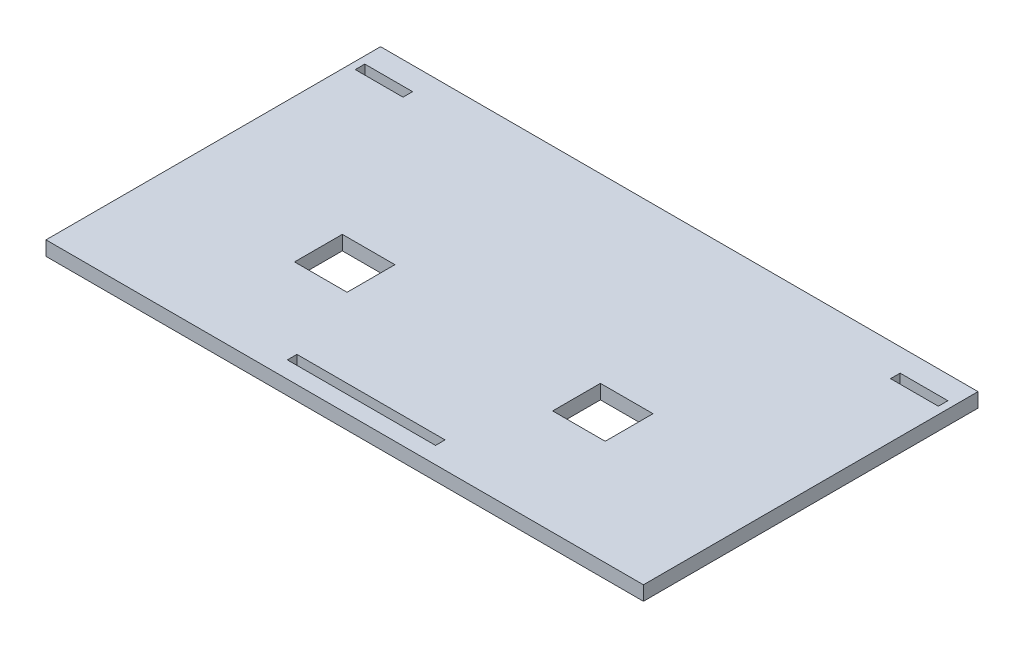
SolidWorks part; units mm, degrees
ref_plane "Alzado" through (0, 0, 0) normal (0, 0, 1) x (1, 0, 0)
ref_plane "Planta" through (0, 0, 0) normal (0, 1, 0) x (1, 0, 0)
ref_plane "Vista lateral" through (0, 0, 0) normal (1, 0, 0) x (0, 0, -1)
sketch "Croquis1" plane through (0, 0, 0) normal (0, 1, 0) x (1, 0, 0)
  line L1 (62.5, 35) -> (-62.5, 35)
  line L2 (62.5, 35) -> (62.5, -35)
  line L3 (62.5, -35) -> (-62.5, -35)
  line L4 (-62.5, 35) -> (-62.5, -35)
  line L5 (62.5, 35) -> (-62.5, -35) construction
  line L6 (62.5, -35) -> (-62.5, 35) construction
  point P0 (0, 0)
  dimension "D1" = 125
  dimension "D2" = 70
extrude "Saliente-Extruir1" add sketch "Croquis1" along normal blind 3
sketch "Croquis2" plane through (0, 3, 0) normal (0, 1, 0) x (1, 0, 0)
  line L0 (62.5, -35) -> (62.5, 35) construction
  line L1 (-61, 30.2) -> (-51, 30.2)
  line L2 (-61, 30.2) -> (-61, 28.2)
  line L3 (-61, 28.2) -> (-51, 28.2)
  line L4 (61, 30.2) -> (61, 28.2)
  line L5 (-62.5, 35) -> (-62.5, -35) construction
  line L6 (62.5, 35) -> (-62.5, 35) construction
  line L7 (51, 30.2) -> (61, 30.2)
  line L9 (-51, 30.2) -> (-51, 28.2)
  line L11 (51, 30.2) -> (51, 28.2)
  line L12 (51, 28.2) -> (61, 28.2)
  dimension "D1" = 2
  dimension "D2" = 1.5
  dimension "D3" = 1.5
  dimension "D4" = 4.8
  dimension "D5" = 10
  dimension "D6" = 10
extrude "Cortar-Extruir1" cut sketch "Croquis2" against normal blind 10
sketch "Croquis3" plane through (0, 3, 0) normal (0, 1, 0) x (1, 0, 0)
  line L0 (-62.5, -35) -> (62.5, -35) construction
  line L1 (-15.5, -31.5) -> (15.5, -31.5)
  line L3 (-15.5, -29.5) -> (15.5, -29.5)
  line L11 (-15.5, -29.5) -> (-15.5, -31.5)
  line L15 (15.5, -31.5) -> (15.5, -29.5)
  dimension "D2" = 3.5
extrude "Cortar-Extruir2" cut sketch "Croquis3" against normal blind 10
sketch "Croquis4" plane through (0, 3, 0) normal (0, 1, 0) x (1, 0, 0)
  line L0 (-62.5, 35) -> (-62.5, -35) construction
  line L1 (-32.5, -3) -> (-21.5, -3)
  line L2 (-32.5, -3) -> (-32.5, -13)
  line L3 (-32.5, -13) -> (-21.5, -13)
  line L4 (32.5, -3) -> (32.5, -13)
  line L5 (62.5, -35) -> (62.5, 35) construction
  line L6 (-62.5, -35) -> (62.5, -35) construction
  line L7 (21.5, -3) -> (32.5, -3)
  line L9 (-21.5, -3) -> (-21.5, -13)
  line L11 (21.5, -3) -> (21.5, -13)
  line L12 (21.5, -13) -> (32.5, -13)
  dimension "D1" = 30
  dimension "D2" = 30
  dimension "D3" = 10
  dimension "D4" = 22
  dimension "D5" = 11
  dimension "D6" = 11
extrude "Cortar-Extruir3" cut sketch "Croquis4" against normal blind 10
